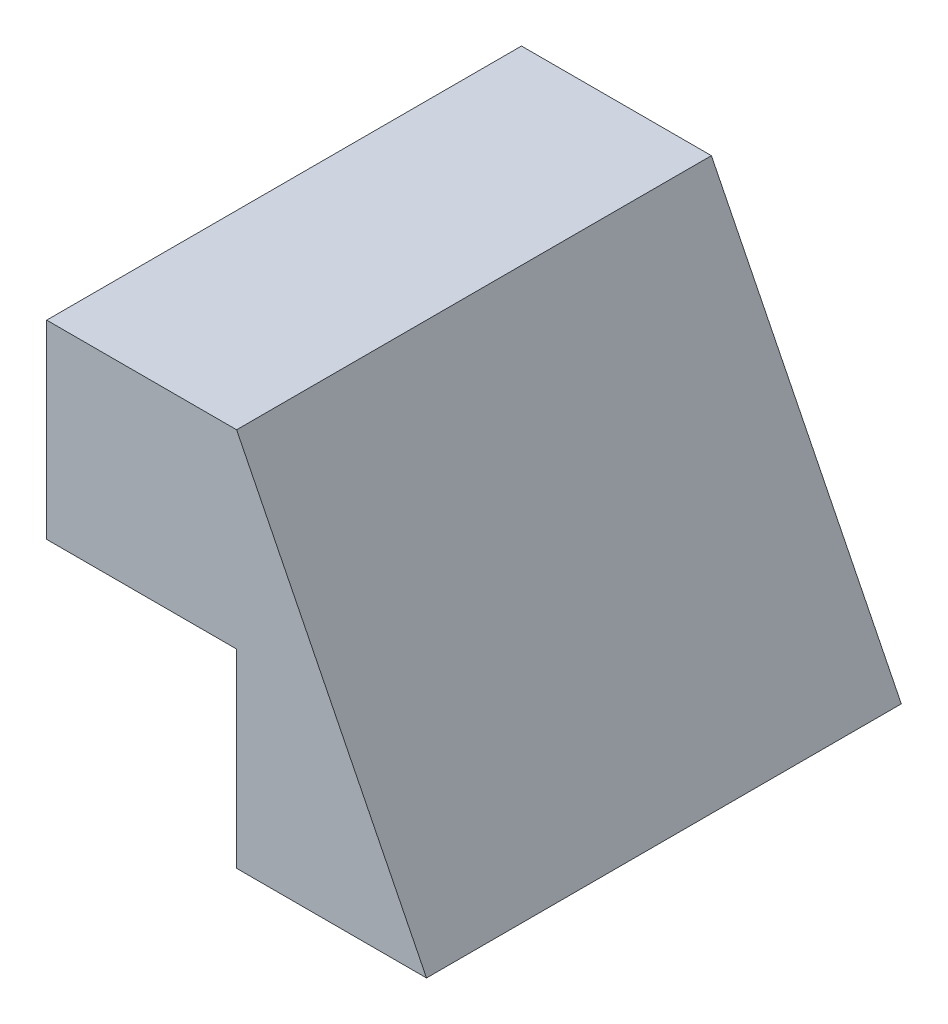
SolidWorks part; units mm, degrees
ref_plane "Front Plane" through (0, 0, 0) normal (0, 0, 1) x (1, 0, 0)
ref_plane "Top Plane" through (0, 0, 0) normal (0, 1, 0) x (1, 0, 0)
ref_plane "Right Plane" through (0, 0, 0) normal (1, 0, 0) x (0, 0, -1)
sketch "Sketch1" plane through (0, 0, 0) normal (0, 0, 1) x (1, 0, 0)
  line L0 (-10, 20) -> (0, 20)
  line L1 (0, 20) -> (10, 0)
  line L2 (10, 0) -> (0, 0)
  line L3 (0, 0) -> (0, 10)
  line L4 (0, 10) -> (-10, 10)
  line L5 (-10, 10) -> (-10, 20)
  dimension "D1" = 10
  dimension "D2" = 10
  dimension "D3" = 10
  dimension "D4" = 10
  dimension "D5" = 10
extrude "Boss-Extrude1" add sketch "Sketch1" along normal blind 25
